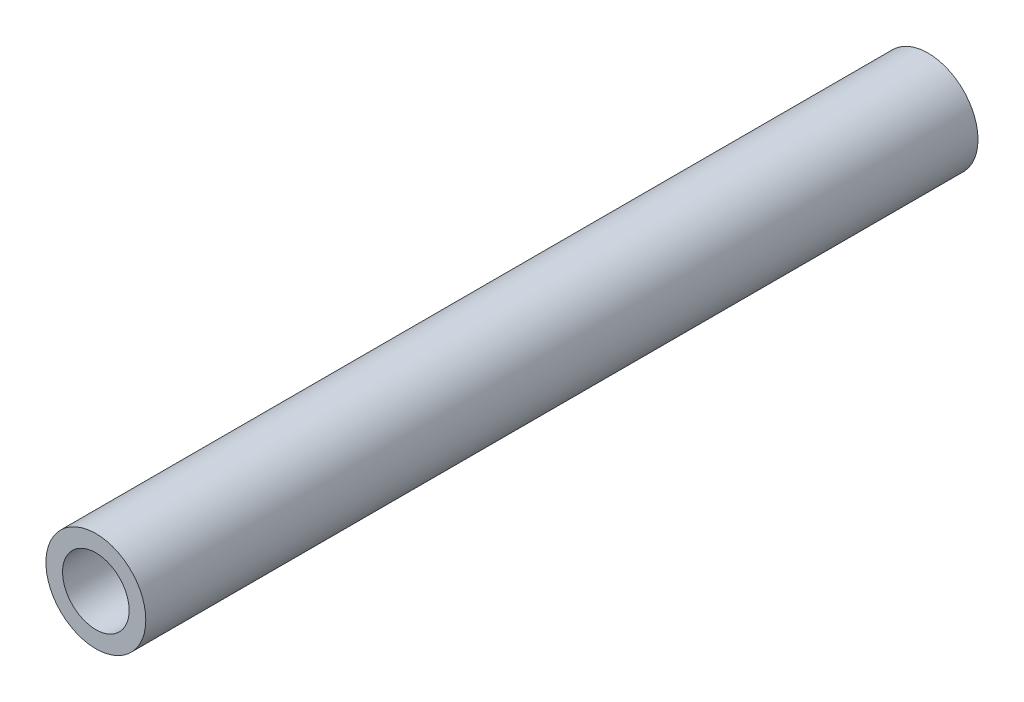
SolidWorks part; units mm, degrees
material "Thornel Mat VMA"
ref_plane "Front Plane" through (0, 0, 0) normal (0, 0, 1) x (1, 0, 0)
ref_plane "Top Plane" through (0, 0, 0) normal (0, 1, 0) x (1, 0, 0)
ref_plane "Right Plane" through (0, 0, 0) normal (1, 0, 0) x (0, 0, -1)
sketch "Sketch1" plane through (0, 0, 0) normal (0, 0, 1) x (1, 0, 0)
  circle A0 centre (0, 0) radius 3
  circle A1 centre (0, 0) radius 2
  dimension "D1" = 6
  dimension "D2" = 1
extrude "Boss-Extrude1" add sketch "Sketch1" along normal blind 50
